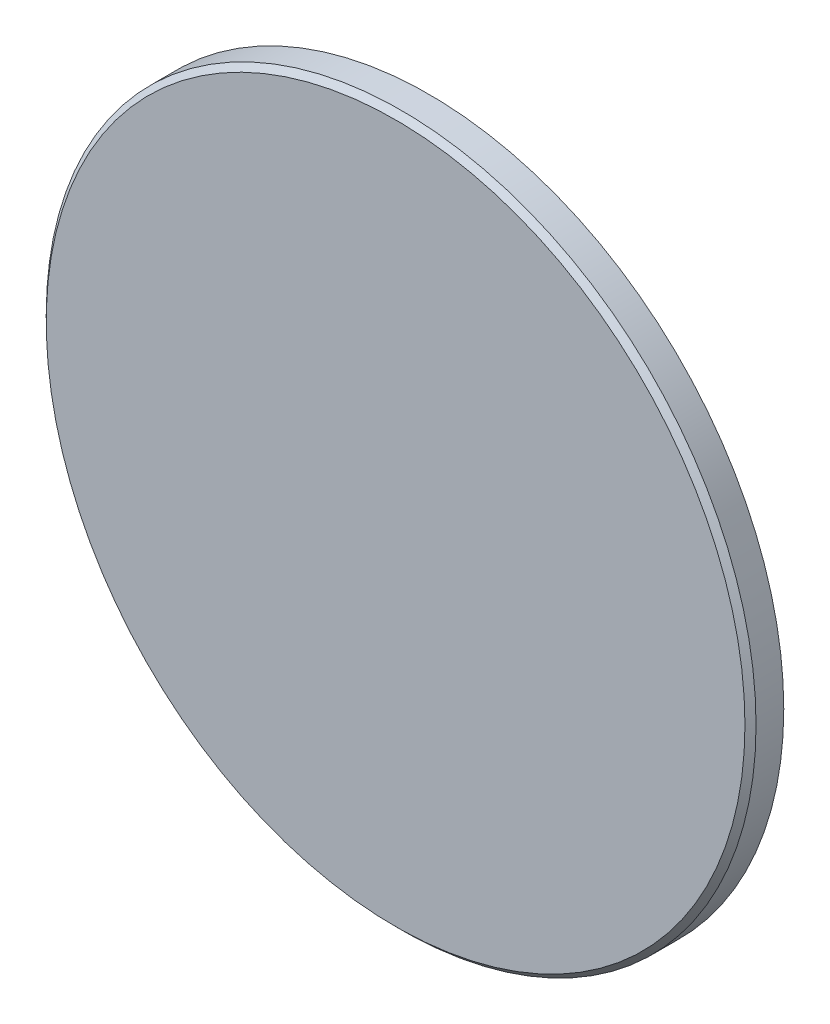
SolidWorks part; units mm, degrees
ref_plane "Front Plane" through (0, 0, 0) normal (0, 0, 1) x (1, 0, 0)
ref_plane "Top Plane" through (0, 0, 0) normal (0, 1, 0) x (1, 0, 0)
ref_plane "Right Plane" through (0, 0, 0) normal (1, 0, 0) x (0, 0, -1)
sketch "Sketch1" plane through (0, 0, 0) normal (0, 0, 1) x (1, 0, 0)
  circle A0 centre (0, 0) radius 16
  dimension "D1" = 32
extrude "Boss-Extrude1" add sketch "Sketch1" along normal blind 1.5
chamfer "Chamfer1" distance 0.25 angle 45 1 edges at (16, 0, 1.5)
